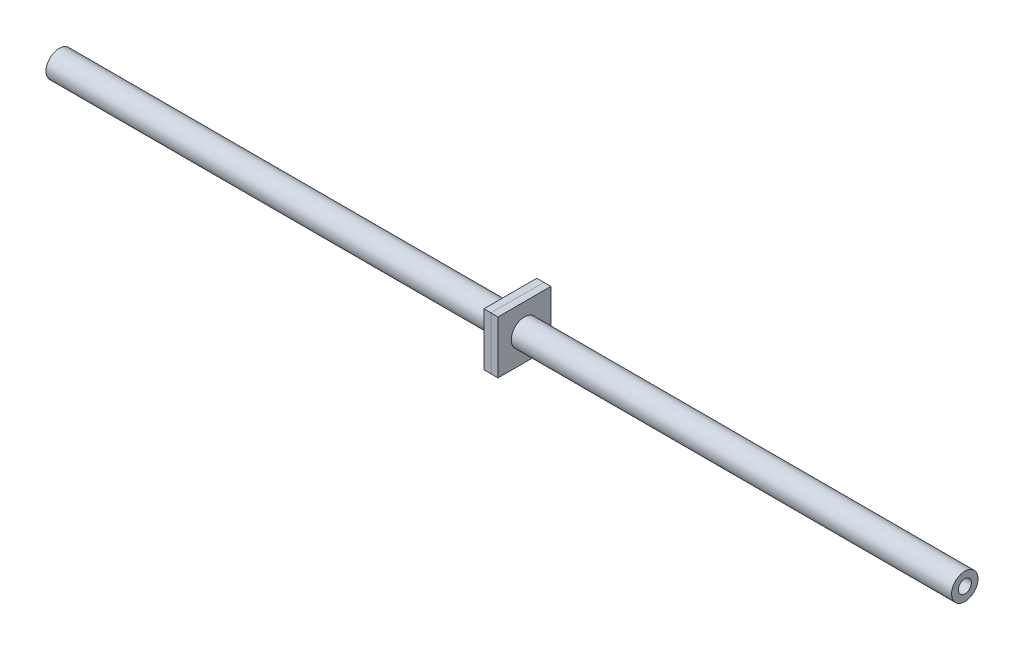
SolidWorks part; units mm, degrees
material "AISI 4130 Steel, normalized at 870C"
ref_plane "Front Plane" through (0, 0, 0) normal (0, 0, 1) x (1, 0, 0)
ref_plane "Top Plane" through (0, 0, 0) normal (0, 1, 0) x (1, 0, 0)
ref_plane "Right Plane" through (0, 0, 0) normal (1, 0, 0) x (0, 0, -1)
sketch "Steering Rod" plane through (0, 0, 0) normal (0, 0, 1) x (1, 0, 0)
  line L0 (0, 0) -> (326.3108, 0)
  line L1 (0, 0) -> (-26.9748, 0) construction
  line L2 (326.3108, 0) -> (353.2856, 0) construction
  dimension "D1" = 26.9748
  dimension "D2" = 380.2604
other "Steering Rod Member"
ref_plane "Plane1" through (0, 0, 0) normal (1, 0, 0) x (0, 1, 0)
sketch "Sketch1" plane through (0, 0, 0) normal (1, 0, 0) x (0, 1, 0)
  circle A0 centre (0, 0) radius 4.7625
  circle A1 centre (0, 0) radius 2.3495
  point P3 (0, 0)
  dimension "D1" = 9.525
  dimension "D2" = 2.413
sketch "Sketch2" plane through (0, 0, 0) normal (1, 0, 0) x (0, 0, -1)
  line L1 (9.525, 9.525) -> (-9.525, 9.525)
  line L2 (9.525, 9.525) -> (9.525, -9.525)
  line L3 (9.525, -9.525) -> (-9.525, -9.525)
  line L4 (-9.525, 9.525) -> (-9.525, -9.525)
  line L5 (9.525, 9.525) -> (-9.525, -9.525) construction
  line L6 (9.525, -9.525) -> (-9.525, 9.525) construction
  circle A0 centre (0, 0) radius 4.7625 construction
  circle A1 centre (0, 0) radius 4.7625
  point P0 (0, 0)
  dimension "D1" = 19.05
extrude "Steering Rod Nut 1" add sketch "Sketch2" along normal blind 2.54 from offset 165.1 separate body
sketch "Sketch3" plane through (0, 0, 0) normal (1, 0, 0) x (0, 0, -1)
  line L0 (9.525, 9.525) -> (-9.525, 9.525) construction
  line L1 (9.525, 9.525) -> (9.525, -9.525) construction
  line L2 (9.525, -9.525) -> (-9.525, -9.525) construction
  line L3 (-9.525, 9.525) -> (-9.525, -9.525) construction
  line L4 (9.525, 9.525) -> (-9.525, 9.525)
  line L5 (9.525, 9.525) -> (9.525, -9.525)
  line L6 (9.525, -9.525) -> (-9.525, -9.525)
  line L7 (-9.525, 9.525) -> (-9.525, -9.525)
  circle A0 centre (0, 0) radius 4.7625 construction
  circle A1 centre (0, 0) radius 4.7625
extrude "Steering Rod Nut 2" add sketch "Sketch3" against normal blind 2.54 from surface at 165.1 separate body starting at face at (165.1, 0, 0)
